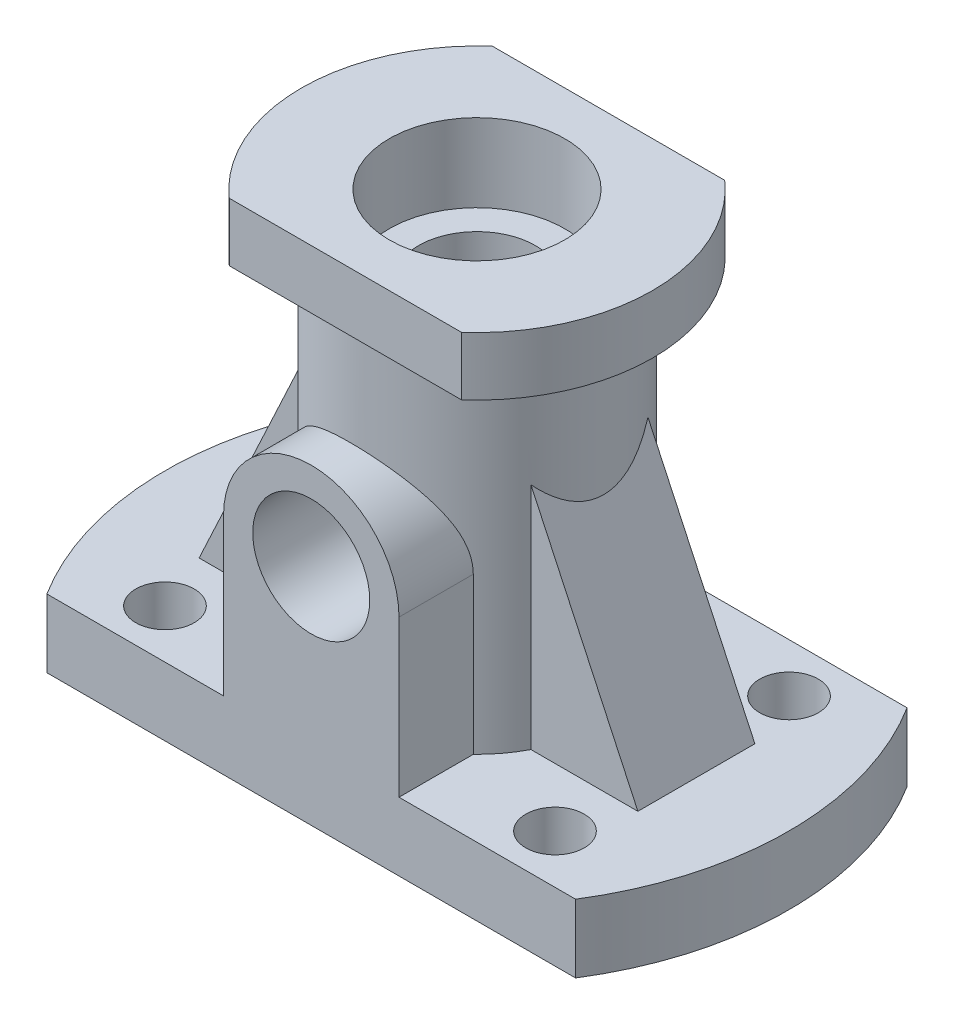
SolidWorks part; units mm, degrees
ref_plane "前视基准面" through (0, 0, 0) normal (0, 0, 1) x (1, 0, 0)
ref_plane "上视基准面" through (0, 0, 0) normal (0, 1, 0) x (1, 0, 0)
ref_plane "右视基准面" through (0, 0, 0) normal (1, 0, 0) x (0, 0, -1)
sketch "草图1" plane through (0, 0, 0) normal (0, 1, 0) x (1, 0, 0)
  line L0 (-27.1109, 17) -> (27.1109, 17)
  line L1 (-27.1109, -17) -> (27.1109, -17)
  arc A0 (-27.1109, 17) -> (-27.1109, -17) centre (0, 0) ccw
  arc A1 (27.1109, -17) -> (27.1109, 17) centre (0, 0) ccw
  dimension "D1" = 64
  dimension "D2" = 17
  dimension "D3" = 34
extrude "凸台-拉伸1" add sketch "草图1" along normal blind 7
sketch "草图2" plane through (0, 7, 0) normal (0, 1, 0) x (1, 0, 0)
  line L0 (-3.85, 0) -> (3.85, 0) construction
  line L1 (0, -3.85) -> (0, 3.85) construction
  circle A0 centre (-20, -12) radius 3
  point P2 (0, 0)
  point P7 (-23.7498, -6.9872)
  point P8 (0, 0)
  point P9 (0, 0)
  dimension "D1" = 6
  dimension "D2" = 12
  dimension "D3" = 20
extrude "切除-拉伸1" cut sketch "草图2" against normal through all
mirror "镜向1" about plane through (0, 0, 0) normal (1, 0, 0) of "切除-拉伸1"
mirror "镜向2" about plane through (0, 0, 0) normal (0, 0, 1) of "镜向1", "切除-拉伸1"
sketch "草图3" plane through (0, 7, 0) normal (0, 1, 0) x (1, 0, 0)
  circle A0 centre (0, 0) radius 13
  dimension "D1" = 26
extrude "凸台-拉伸2" add sketch "草图3" along normal blind 35
sketch "草图4" plane through (0, 42, 0) normal (0, 1, 0) x (1, 0, 0)
  line L0 (-11.9059, 13.5) -> (11.9059, 13.5)
  line L1 (11.9059, -13.5) -> (-11.9059, -13.5)
  line L2 (-23.1, 0) -> (23.1, 0) construction
  arc A0 (-11.9059, 13.5) -> (-11.9059, -13.5) centre (0, 0) ccw
  arc A1 (11.9059, -13.5) -> (11.9059, 13.5) centre (0, 0) ccw
  dimension "D1" = 36
  dimension "D2" = 13.5
  dimension "D3" = 27
extrude "凸台-拉伸3" add sketch "草图4" along normal blind 6
sketch "草图5" plane through (0, 48, 0) normal (0, 1, 0) x (1, 0, 0)
  circle A0 centre (0, 0) radius 9
  dimension "D1" = 18
extrude "切除-拉伸2" cut sketch "草图5" against normal blind 8
sketch "草图6" plane through (0, 40, 0) normal (0, 1, 0) x (1, 0, 0)
  circle A0 centre (0, 0) radius 6
  dimension "D1" = 12
extrude "切除-拉伸3" cut sketch "草图6" against normal through all
sketch "草图7" plane through (0, 0, 17) normal (0, 0, 1) x (1, 0, 0)
  line L0 (0, -18.7) -> (0, 18.7) construction
  line L1 (-9, 23) -> (-9, 0)
  line L2 (18.7, 0) -> (-18.7, 0) construction
  line L3 (-9, 0) -> (9, 0)
  line L4 (9, 0) -> (9, 23)
  arc A0 (9, 23) -> (-9, 23) centre (0, 23) ccw
  dimension "D1" = 18
  dimension "D2" = 23
extrude "凸台-拉伸4" add sketch "草图7" against normal up to next
sketch "草图8" plane through (0, 0, 17) normal (0, 0, 1) x (1, 0, 0)
  line L0 (0, -18.7) -> (0, 18.7) construction
  circle A0 centre (0, 23) radius 6
  dimension "D1" = 12
  dimension "D2" = 23
extrude "切除-拉伸4" cut sketch "草图8" against normal up to next
sketch "草图9" plane through (0, 0, 0) normal (0, 0, 1) x (1, 0, 0)
  line L0 (-22.5, 7) -> (-11.0867, 7)
  line L1 (-27.1109, 7) -> (-9, 7) construction
  line L2 (-11.0867, 7) -> (-11.0867, 31.476)
  line L3 (-11.0867, 31.476) -> (-22.5, 7)
  line L4 (0, -18.7) -> (0, 18.7) construction
  dimension "D1" = 22.5
  dimension "D2" = 65
extrude "凸台-拉伸5" add sketch "草图9" along normal blind 6 and the other way blind 6
mirror "镜向3" about plane through (0, 0, 0) normal (1, 0, 0) of "凸台-拉伸5"
